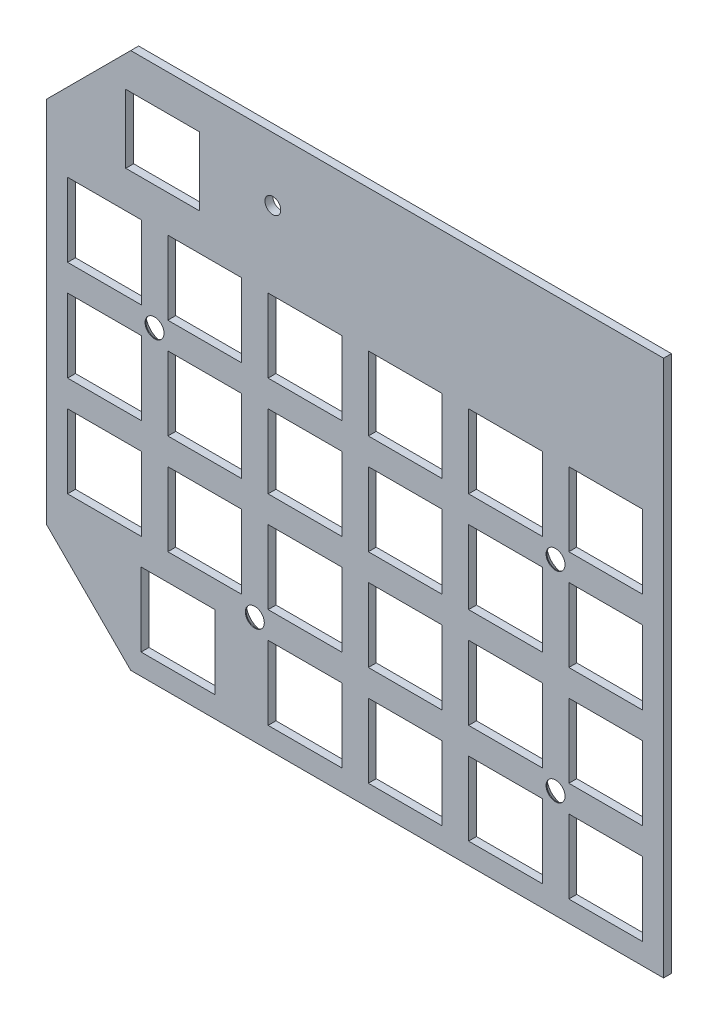
SolidWorks part; units mm, degrees
material "Alliage 1060"
ref_plane "Plan de face" through (0, 0, 0) normal (0, 0, 1) x (1, 0, 0)
ref_plane "Plan de dessus" through (0, 0, 0) normal (0, 1, 0) x (1, 0, 0)
ref_plane "Plan de droite" through (0, 0, 0) normal (1, 0, 0) x (0, 0, -1)
sketch "Esquisse1" plane through (0, 0, 0) normal (0, 0, 1) x (1, 0, 0)
  line L0 (0, -85) -> (16, -101)
  line L4 (117.25, 1) -> (117.25, -101)
  line L5 (16, 1) -> (0, -15)
  line L7 (117.25, 1) -> (16, 1)
  line L8 (0, -15) -> (0, -85)
  line L9 (16, -101) -> (117.25, -101)
  dimension "D1" = 102
  dimension "D2" = 117.25
  dimension "D3" = 16
  dimension "D4" = 16
  dimension "D5" = 16
  dimension "D6" = 16
extrude "Boss.-Extru.1" add sketch "Esquisse1" along normal blind 1.5
sketch "Esquisse3" plane through (0, 0, 0) normal (0, 0, -1) x (-1, 0, 0)
  line L0 (-94.2, -25.85) -> (-94.2, -39.85)
  line L1 (-113.25, -25.85) -> (-99.25, -25.85)
  line L2 (-113.25, -25.85) -> (-113.25, -39.85)
  line L3 (-113.25, -39.85) -> (-99.25, -39.85)
  line L4 (-99.25, -25.85) -> (-99.25, -39.85)
  line L5 (-106.25, -39.85) -> (-106.25, -25.85) construction
  line L6 (-113.25, -32.85) -> (-99.25, -32.85) construction
  line L7 (-94.2, -25.85) -> (-80.2, -25.85)
  line L8 (-80.2, -25.85) -> (-80.2, -39.85)
  line L9 (-94.2, -39.85) -> (-80.2, -39.85)
  line L10 (-75.15, -25.85) -> (-75.15, -39.85)
  line L11 (-75.15, -25.85) -> (-61.15, -25.85)
  line L12 (-61.15, -25.85) -> (-61.15, -39.85)
  line L13 (-75.15, -39.85) -> (-61.15, -39.85)
  line L14 (-56.1, -25.85) -> (-56.1, -39.85)
  line L15 (-56.1, -25.85) -> (-42.1, -25.85)
  line L16 (-42.1, -25.85) -> (-42.1, -39.85)
  line L17 (-56.1, -39.85) -> (-42.1, -39.85)
  line L18 (-37.05, -25.85) -> (-37.05, -39.85)
  line L19 (-37.05, -25.85) -> (-23.05, -25.85)
  line L20 (-23.05, -25.85) -> (-23.05, -39.85)
  line L21 (-37.05, -39.85) -> (-23.05, -39.85)
  line L22 (-18, -25.85) -> (-18, -39.85)
  line L23 (-18, -25.85) -> (-4, -25.85)
  line L24 (-4, -25.85) -> (-4, -39.85)
  line L25 (-18, -39.85) -> (-4, -39.85)
  line L26 (-94.2, -44.9) -> (-94.2, -58.9)
  line L27 (-94.2, -44.9) -> (-80.2, -44.9)
  line L28 (-80.2, -44.9) -> (-80.2, -58.9)
  line L29 (-94.2, -58.9) -> (-80.2, -58.9)
  line L30 (-75.15, -44.9) -> (-75.15, -58.9)
  line L31 (-75.15, -44.9) -> (-61.15, -44.9)
  line L32 (-61.15, -44.9) -> (-61.15, -58.9)
  line L33 (-75.15, -58.9) -> (-61.15, -58.9)
  line L34 (-56.1, -44.9) -> (-56.1, -58.9)
  line L35 (-56.1, -44.9) -> (-42.1, -44.9)
  line L36 (-42.1, -44.9) -> (-42.1, -58.9)
  line L37 (-56.1, -58.9) -> (-42.1, -58.9)
  line L38 (-37.05, -44.9) -> (-37.05, -58.9)
  line L39 (-37.05, -44.9) -> (-23.05, -44.9)
  line L40 (-23.05, -44.9) -> (-23.05, -58.9)
  line L41 (-37.05, -58.9) -> (-23.05, -58.9)
  line L42 (-18, -44.9) -> (-18, -58.9)
  line L43 (-18, -44.9) -> (-4, -44.9)
  line L44 (-4, -44.9) -> (-4, -58.9)
  line L45 (-18, -58.9) -> (-4, -58.9)
  line L46 (-94.2, -63.95) -> (-94.2, -77.95)
  line L47 (-94.2, -63.95) -> (-80.2, -63.95)
  line L48 (-80.2, -63.95) -> (-80.2, -77.95)
  line L49 (-94.2, -77.95) -> (-80.2, -77.95)
  line L50 (-75.15, -63.95) -> (-75.15, -77.95)
  line L51 (-75.15, -63.95) -> (-61.15, -63.95)
  line L52 (-61.15, -63.95) -> (-61.15, -77.95)
  line L53 (-75.15, -77.95) -> (-61.15, -77.95)
  line L54 (-56.1, -63.95) -> (-56.1, -77.95)
  line L55 (-56.1, -63.95) -> (-42.1, -63.95)
  line L56 (-42.1, -63.95) -> (-42.1, -77.95)
  line L57 (-56.1, -77.95) -> (-42.1, -77.95)
  line L58 (-37.05, -63.95) -> (-37.05, -77.95)
  line L59 (-37.05, -63.95) -> (-23.05, -63.95)
  line L60 (-23.05, -63.95) -> (-23.05, -77.95)
  line L61 (-37.05, -77.95) -> (-23.05, -77.95)
  line L62 (-18, -63.95) -> (-18, -77.95)
  line L63 (-18, -63.95) -> (-4, -63.95)
  line L64 (-4, -63.95) -> (-4, -77.95)
  line L65 (-18, -77.95) -> (-4, -77.95)
  line L66 (-94.2, -83) -> (-94.2, -97)
  line L67 (-94.2, -83) -> (-80.2, -83)
  line L68 (-80.2, -83) -> (-80.2, -97)
  line L69 (-94.2, -97) -> (-80.2, -97)
  line L70 (-75.15, -83) -> (-75.15, -97)
  line L71 (-75.15, -83) -> (-61.15, -83)
  line L72 (-61.15, -83) -> (-61.15, -97)
  line L73 (-75.15, -97) -> (-61.15, -97)
  line L74 (-56.1, -83) -> (-56.1, -97)
  line L75 (-56.1, -83) -> (-42.1, -83)
  line L76 (-42.1, -83) -> (-42.1, -97)
  line L77 (-56.1, -97) -> (-42.1, -97)
  line L86 (-113.25, -44.9) -> (-113.25, -58.9)
  line L87 (-113.25, -44.9) -> (-99.25, -44.9)
  line L88 (-99.25, -44.9) -> (-99.25, -58.9)
  line L89 (-113.25, -58.9) -> (-99.25, -58.9)
  line L90 (-113.25, -63.95) -> (-113.25, -77.95)
  line L91 (-113.25, -63.95) -> (-99.25, -63.95)
  line L92 (-99.25, -63.95) -> (-99.25, -77.95)
  line L93 (-113.25, -77.95) -> (-99.25, -77.95)
  line L94 (-113.25, -83) -> (-113.25, -97)
  line L95 (-113.25, -83) -> (-99.25, -83)
  line L96 (-99.25, -83) -> (-99.25, -97)
  line L97 (-113.25, -97) -> (-99.25, -97)
  line L98 (-4, -83) -> (-4, -97) [skipped]
  line L99 (-18, -97) -> (-4, -97) [skipped]
  line L100 (-18, -83) -> (-18, -97) [skipped]
  line L101 (-18, -83) -> (-4, -83) [skipped]
  line L103 (-117.25, -101) -> (-117.25, 1) construction
  line L104 (-16, -101) -> (-117.25, -101) construction
  line L107 (-37.05, -83) -> (-23.05, -83) [skipped]
  line L108 (-23.05, -83) -> (-23.05, -97) [skipped]
  line L109 (-37.05, -83) -> (-37.05, -97) [skipped]
  line L110 (-37.05, -97) -> (-23.05, -97) [skipped]
  line L111 (0, -15) -> (0, -85) construction
  line L112 (-31.97, -83) -> (-17.97, -83)
  line L113 (-31.97, -83) -> (-31.97, -97)
  line L114 (-31.97, -97) -> (-17.97, -97)
  line L115 (-17.97, -83) -> (-17.97, -97)
  line L116 (-24.97, -97) -> (-24.97, -83) construction
  line L117 (-31.97, -90) -> (-17.97, -90) construction
  line L118 (-29.05, -5.85) -> (-15.05, -5.85)
  line L119 (-29.05, -5.85) -> (-29.05, -18.85)
  line L120 (-29.05, -18.85) -> (-15.05, -18.85)
  line L121 (-15.05, -5.85) -> (-15.05, -18.85)
  line L122 (-117.25, 1) -> (-16, 1) construction
  circle A5 centre (-43, -11) radius 1.5
  point P0 (-106.25, -32.85)
  point P84 (-24.97, -90)
  dimension "D7" = 43
  dimension "D8" = 12
  dimension "D1" = 14
  dimension "D2" = 14
  dimension "D5" = 4
  dimension "D6" = 4
  dimension "D9" = 5.05
  dimension "D10" = 14
  dimension "D11" = 14
  dimension "D12" = 10.13
  dimension "D13" = 5.05
  dimension "D14" = 14
  dimension "D15" = 7
  dimension "D16" = 13
  dimension "D17" = 6
  dimension "D3" = 6
  dimension "D4" = 4
extrude "Enlèv. mat.-Extru.2" cut sketch "Esquisse3" against normal blind 10
sketch "Esquisse4" plane through (0, 0, 0) normal (0, 0, -1) x (-1, 0, 0)
  line L0 (-99.25, -39.85) -> (-94.2, -44.9) construction
  line L1 (-23.05, -39.85) -> (-18, -44.9) construction
  line L2 (-37.05, -77.95) -> (-42.1, -83) construction
  line L3 (-94.2, -77.95) -> (-99.25, -83) construction
  point P16 (-96.725, -42.375)
  point P17 (-96.725, -80.475)
  point P18 (-39.575, -80.475)
hole_wizard "Fraisage pour vis à tête fraisée M31" positions "Esquisse5" profile "Esquisse6" countersink size "M3" standard "Ansi Metric" end condition through all
sketch "Esquisse5" plane through (0, 0, 0) normal (0, 0, -1) x (-1, 0, 0)
  line L0 (-23.05, -39.85) -> (-18, -44.9) construction
  line L1 (-37.05, -77.95) -> (-42.1, -83) construction
  point P0 (-96.725, -42.375)
  point P3 (-96.725, -80.475)
  point P6 (-20.525, -42.375)
  point P10 (-39.575, -80.475)
sketch "Esquisse6" plane through (96.725, -42.375, 0) normal (1, 0, 0) x (0, 1, 0)
  line L0 (0, 0) -> (0, 1.5)
  line L1 (0, 1.5) -> (1.8, 1.5)
  line L2 (1.8, 1.5) -> (1.8, 1.35)
  line L3 (1.8, 1.35) -> (3.15, 0)
  line L5 (3.15, 0) -> (0, 0)
  line L6 (-1.8, 1.35) -> (-3.15, 0) construction
  line L11 (0, -6.35) -> (0, 107.95) construction
  dimension "Diamètre du perçage jusqu'au prochain" = 3.6
  dimension "Profondeur du perçage jusqu'au prochain" = 1.5
  dimension "Diamètre du fraisage entrant" = 6.3
  dimension "Angle du fraisage entrant" = 90
